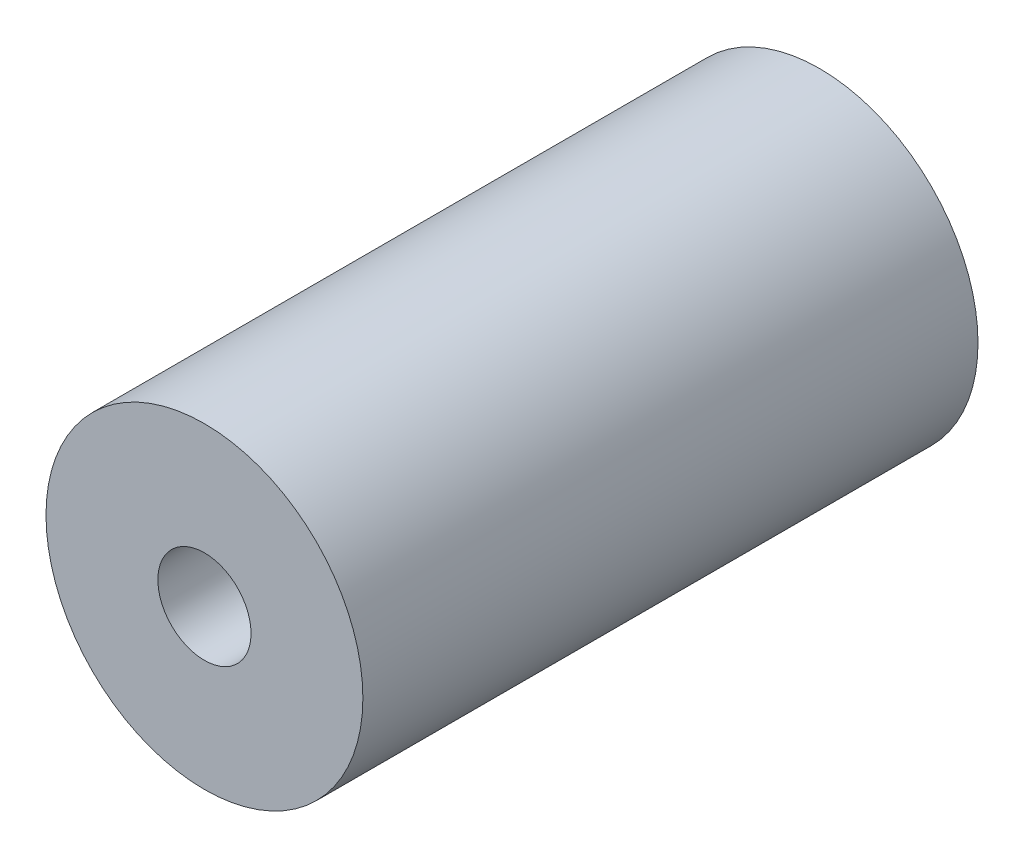
SolidWorks part; units mm, degrees
ref_plane "Alzado" through (0, 0, 0) normal (0, 0, 1) x (1, 0, 0)
ref_plane "Planta" through (0, 0, 0) normal (0, 1, 0) x (1, 0, 0)
ref_plane "Vista lateral" through (0, 0, 0) normal (1, 0, 0) x (0, 0, -1)
sketch "Croquis1" plane through (0, 0, 0) normal (0, 0, 1) x (1, 0, 0)
  circle A0 centre (0, 0) radius 17
  circle A1 centre (0, 0) radius 5
  dimension "D1" = 34
  dimension "D2" = 10
extrude "Saliente-Extruir1" add sketch "Croquis1" along normal mid plane 66
